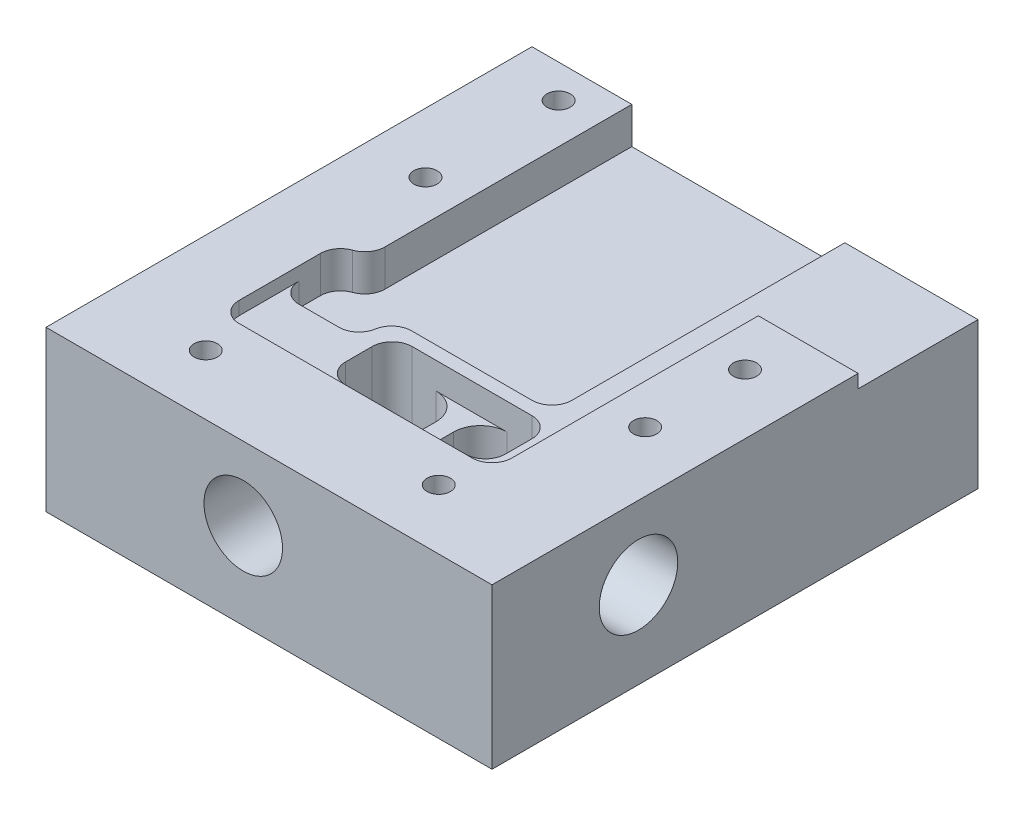
SolidWorks part; units mm, degrees
ref_plane "Front" through (0, 0, 0) normal (0, 0, 1) x (1, 0, 0)
ref_plane "Top" through (0, 0, 0) normal (0, 1, 0) x (1, 0, 0)
ref_plane "Right" through (0, 0, 0) normal (1, 0, 0) x (0, 0, -1)
sketch "Sketch1" plane through (0, 0, 0) normal (0, 1, 0) x (1, 0, 0)
  line L1 (0, 0) -> (67, 0)
  line L2 (0, 0) -> (0, 73)
  line L3 (0, 73) -> (67, 73)
  line L4 (67, 0) -> (67, 73)
  dimension "D1" = 73
  dimension "D2" = 67
extrude "Boss-Extrude1" add sketch "Sketch1" along normal blind 15
sketch "Sketch5" plane through (0, 15, 0) normal (0, 1, 0) x (1, 0, 0)
  line L0 (18.5, 15) -> (11, 15)
  line L1 (32, 15) -> (52, 15)
  line L2 (47, 73) -> (47, 29)
  line L3 (47, 73) -> (52, 73)
  line L4 (52, 15) -> (52, 73)
  line L5 (47, 29) -> (23, 29)
  line L7 (0, 0) -> (67, 0) construction
  line L8 (11, 24) -> (14.7889, 24)
  line L9 (67, 0) -> (67, 73) construction
  line L10 (11, 15) -> (11, 24)
  line L11 (18.5, 15) -> (32, 15)
  line L12 (23, 29) -> (23, 27)
  line L13 (20, 24) -> (14.7889, 24)
  arc A0 (23, 27) -> (20, 24) centre (20, 27) cw
  point P17 (17.932, 24.0268)
  point P19 (18.3944, 28)
  dimension "D6" = 14
  dimension "D5" = 3
  dimension "D1" = 5
  dimension "D2" = 58
  dimension "D3" = 15
  dimension "D4" = 15
  dimension "D7" = 41
  dimension "D8" = 9
  dimension "D10" = 24
extrude "Boss-Extrude2" add sketch "Sketch5" along normal blind 3.5
sketch "Sketch6" plane through (0, 18.5, 0) normal (0, 1, 0) x (1, 0, 0)
  line L1 (25, 27) -> (49, 27)
  line L2 (25, 27) -> (25, 17)
  line L3 (25, 17) -> (49, 17)
  line L4 (49, 27) -> (49, 17)
  line L6 (47, 29) -> (23, 29) construction
  line L8 (11, 15) -> (52, 15) construction
  line L13 (52, 15) -> (52, 73) construction
  dimension "D1" = 2
  dimension "D2" = 2
  dimension "D3" = 24
  dimension "D4" = 3
extrude "Cut-Extrude2" cut sketch "Sketch6" against normal blind 16
sketch "Sketch8" plane through (0, 0, -17) normal (0, 0, -1) x (-1, 0, 0)
  line L4 (-49, 2.5) -> (-25, 2.5)
  line L5 (-25, 18.5) -> (-49, 18.5)
  line L6 (-49, 18.5) -> (-49, 2.5)
  line L7 (-49, 2.5) -> (-25, 2.5)
  line L8 (-25, 2.5) -> (-25, 18.5)
  line L9 (-25, 18.5) -> (-49, 18.5)
  line L10 (-49, 18.5) -> (-49, 2.5) construction
  line L12 (-25, 2.5) -> (-25, 18.5) construction
  circle A0 centre (-42, 6.1554) radius 4
  dimension "D1" = 8
  dimension "D4" = 7
extrude "Cut-Extrude4" [suppressed] cut sketch "Sketch8" against normal through all contours A0
sketch "Sketch9" plane through (49, 0, 0) normal (-1, 0, 0) x (0, 0, 1)
  line L4 (-17, 18.5) -> (-27, 18.5)
  line L5 (-27, 18.5) -> (-27, 2.5)
  line L6 (-27, 2.5) -> (-17, 2.5)
  line L7 (-17, 2.5) -> (-17, 18.5)
  line L8 (-17, 18.5) -> (-27, 18.5)
  line L9 (-27, 18.5) -> (-27, 2.5) construction
  line L10 (-27, 2.5) -> (-17, 2.5)
  line L11 (-17, 2.5) -> (-17, 18.5) construction
  circle A0 centre (-22, 5.8531) radius 4
  dimension "D2" = 8
  dimension "D3" = 5
extrude "Cut-Extrude5" [suppressed] cut sketch "Sketch9" against normal through all contours A0
sketch "Sketch11" plane through (0, 0, 0) normal (0, -1, 0) x (1, 0, 0)
  line L1 (0, 0) -> (67, 0)
  line L2 (0, 0) -> (0, -73)
  line L3 (0, -73) -> (67, -73)
  line L4 (67, 0) -> (67, -73)
extrude "Boss-Extrude4" add sketch "Sketch11" along normal blind 3.5
sketch "Sketch12" plane through (0, 15, 0) normal (0, 1, 0) x (1, 0, 0)
  line L0 (18.4556, 68) -> (48.6562, 68) construction
  line L1 (18.4556, 68) -> (18.4556, 18.1652) construction
  line L2 (67, 73) -> (52, 73) construction
  line L3 (67, 0) -> (67, 73) construction
  circle A0 centre (18.4556, 68) radius 1.025
  circle A2 centre (48.6562, 68) radius 1.025
  circle A4 centre (36.6635, 53.2215) radius 1.38 construction
  circle A6 centre (18.4556, 18.1652) radius 1.025
  dimension "D1" = 2.05
  dimension "D2" = 30.2006
  dimension "D3" = 49.8348
  dimension "D4" = 5
  dimension "D5" = 18.3438
sketch "Sketch13" plane through (0, 15, 0) normal (0, 1, 0) x (1, 0, 0)
  line L1 (52, 15) -> (67, 15)
  line L2 (52, 15) -> (52, 55)
  line L3 (52, 55) -> (67, 55)
  line L4 (67, 15) -> (67, 55)
  line L5 (11, 15) -> (52, 15) construction
  line L7 (67, 0) -> (67, 73) construction
  dimension "D1" = 15
  dimension "D2" = 40
extrude "Boss-Extrude6" add sketch "Sketch13" along normal blind 5.5
sketch "Sketch16" [suppressed] plane through (0, 0, 0) normal (0, 0, 1) x (1, 0, 0)
  circle A0 centre (57, 6.1554) radius 5.9
  circle A1 centre (57, 6.1554) radius 4 construction
  circle A2 centre (57, 6.1554) radius 4 construction
  dimension "D1" = 11.8
extrude "Cut-Extrude8" [suppressed] cut sketch "Sketch16" against normal blind 10
sketch "Sketch17" [suppressed] plane through (67, 0, 0) normal (1, 0, 0) x (0, 0, -1)
  circle A0 centre (65, 5.8531) radius 4 construction
  circle A1 centre (65, 5.8531) radius 4 construction
  circle A2 centre (65, 5.8531) radius 5.9
  dimension "D1" = 11.8
extrude "Cut-Extrude9" [suppressed] cut sketch "Sketch17" against normal blind 10
sketch "Sketch14" plane through (0, 20.5, 0) normal (0, 1, 0) x (1, 0, 0)
  line L0 (67, 15) -> (67, 55) construction
  line L1 (67, 55) -> (52, 55) construction
  circle A0 centre (58, 47) radius 1.75
  circle A1 centre (58, 32) radius 1.75
  dimension "D1" = 3.5
  dimension "D2" = 15
  dimension "D3" = 9
  dimension "D4" = 8
extrude "Cut-Extrude7" cut sketch "Sketch14" against normal blind 10
sketch "Sketch18" plane through (0, 15, 0) normal (0, 1, 0) x (1, 0, 0)
  line L0 (15, 33.2378) -> (15, 73)
  line L1 (67, 15) -> (15, 15)
  line L2 (67, 15) -> (67, 0)
  line L3 (67, 0) -> (0, 0)
  line L4 (0, 15) -> (0, 0)
  line L5 (67, 73) -> (52, 73) construction
  line L6 (15, 73) -> (0, 73)
  line L7 (0, 73) -> (0, 15)
  line L8 (52, 15) -> (52, 55) construction
  line L9 (15, 33.2378) -> (14, 33.2378)
  line L10 (11, 30.2378) -> (11, 17.9921)
  line L12 (13.7825, 15) -> (15, 15)
  arc A0 (14, 33.2378) -> (11, 30.2378) centre (14, 30.2378) ccw
  arc A1 (11, 17.9921) -> (13.7825, 15) centre (14, 17.9921) ccw
  dimension "D2" = 3
  dimension "D1" = 37
  dimension "D3" = 4
extrude "Boss-Extrude7" add sketch "Sketch18" along normal up to surface (5.5 mm away) up to face at (58, 20.5, -30.25)
sketch "Sketch19" plane through (0, 20.5, 0) normal (0, 1, 0) x (1, 0, 0)
  line L0 (9, 68) -> (9, 48) construction
  line L1 (67, 0) -> (0, 0) construction
  line L3 (15, 73) -> (15, 33.2378) construction
  line L4 (52, 15) -> (13.7825, 15) construction
  line L5 (15, 9) -> (50, 9) construction
  line L6 (0, 0) -> (0, 73) construction
  circle A0 centre (9, 48) radius 1.75
  circle A1 centre (9, 68) radius 1.75
  circle A2 centre (15, 9) radius 1.75
  circle A3 centre (50, 9) radius 1.75
  dimension "D1" = 3.5
  dimension "D2" = 3.5
  dimension "D6" = 3.5
  dimension "D7" = 3.5
  dimension "D3" = 20
  dimension "D5" = 6
  dimension "D8" = 35
  dimension "D10" = 15
  dimension "D9" = 9
  dimension "D4" = 33
fillet "Fillet5" radius 3 1 edges at (52, 19.5, -15)
sketch "Sketch20" plane through (0, 15, 0) normal (0, 1, 0) x (1, 0, 0)
  line L4 (52, 55) -> (67, 55)
  line L5 (52, 55) -> (67, 55)
  line L6 (67, 73) -> (52, 73)
  line L7 (67, 55) -> (67, 73)
  line L8 (67, 55) -> (67, 73)
  line L9 (52, 73) -> (52, 55)
  line L10 (67, 73) -> (52, 73)
  line L11 (52, 73) -> (52, 55)
  dimension "D1" = 0
extrude "Boss-Extrude8" add sketch "Sketch20" along normal up to surface (3.5 mm away) up to face at (37, 18.5, -22)
fillet "Fillet10" radius 3 1 edges at (47, 16.75, -29)
fillet "Fillet11" radius 3 2 edges at (23, 16.75, -29) (11, 16.75, -24)
fillet "Fillet12" radius 3 1 edges at (15, 17.75, -33.2378)
fillet "Fillet13" radius 3 4 edges at (25, 10.5, -27) (25, 10.5, -17) (49, 10.5, -27) (49, 10.5, -17)
sketch "Sketch21" plane through (0, 2.5, 0) normal (0, 1, 0) x (1, 0, 0)
  line L0 (46, 27) -> (28, 27) construction
  line L1 (35.5807, 27) -> (38.2299, 27)
  line L2 (35.5807, 27) -> (35.5807, 17)
  line L3 (35.5807, 17) -> (38.2299, 17)
  line L4 (38.2299, 27) -> (38.2299, 17)
  line L5 (28, 17) -> (46, 17) construction
extrude "Boss-Extrude9" add sketch "Sketch21" along normal blind 12
fillet "Fillet15" radius 4 4 edges at (35.5807, 8.5, -27) (38.2299, 8.5, -27) (38.2299, 8.5, -17) (35.5807, 8.5, -17)
extrude "Cut-Extrude11" cut sketch "Sketch19" against normal blind 10
sketch "Sketch23" plane through (49, 0, 0) normal (-1, 0, 0) x (0, 0, 1)
  line L0 (-20, 2.5) -> (-24, 2.5) construction
  line L1 (-22, 18.5) -> (-22, 2.5) construction
  line L2 (-20, 18.5) -> (-24, 18.5) construction
  circle A0 centre (-22, 9.5) radius 4
  point P4 (-22, 2.5)
  dimension "D1" = 8
  dimension "D2" = 7
extrude "Cut-Extrude12" cut sketch "Sketch23" against normal through all and the other way blind 2
sketch "Sketch24" plane through (67, 0, 0) normal (1, 0, 0) x (0, 0, -1)
  circle A0 centre (22, 9.5) radius 5.9
  dimension "D1" = 11.8
extrude "Cut-Extrude13" cut sketch "Sketch24" against normal blind 10
sketch "Sketch25" plane through (0, 0, -17) normal (0, 0, -1) x (-1, 0, 0)
  line L0 (-28, 2.5) -> (-31.5807, 2.5) construction
  circle A0 centre (-29.6283, 9.5) radius 4
  dimension "D1" = 8
  dimension "D2" = 7
extrude "Cut-Extrude14" cut sketch "Sketch25" against normal through all and the other way blind 2
sketch "Sketch26" plane through (0, 0, 0) normal (0, 0, 1) x (1, 0, 0)
  circle A0 centre (29.6283, 9.5) radius 5.9
  dimension "D1" = 11.8
extrude "Cut-Extrude15" cut sketch "Sketch26" against normal blind 10
ref_plane "Plane1" through (52, 18.5, -55) normal (0, -1, 0) x (-1, 0, 0)
equation "\"d_racor\"= 11.8"
equation "\"h_alphasense\"= 5"
equation "\"h_chamber\"= 13"
equation "\"d_alphasense\"= 32.4mm"
equation "\"d_chamber\"= 19"
equation "\"h_base\"= 25 - \"h_chamber\" - \"h_alphasense\"-1"
equation "\"length_thread\"=10"
equation "\"D2@Sketch9\"=\"d_pipe\""
equation "\"D1@Sketch8\"=\"d_pipe\""
equation "\"length_racor\"= 10"
equation "\"d_pipe\"=8"
equation "\"D1@Sketch12\"= \"d_thread_sck_tap\""
equation "\"D1@Sketch16\"=\"d_racor\""
equation "\"D1@Cut-Extrude8\"=\"length_racor\""
equation "\"D1@Sketch17\"=\"d_racor\""
equation "\"D1@Cut-Extrude9\"=\"length_racor\""
equation "\"clip_thread_hole\"= 4"
equation "\"clip_thread_tap_drill\"= 3.5"
equation "\"D1@Sketch14\"=\"clip_thread_tap_drill\""
equation "\"D1@Cut-Extrude7\"=\"length_thread\""
equation "\"d_thread_sck_hole\"= 2.5"
equation "\"d_thread_sck_tap\"= 2.05"
equation "\"D1@Sketch19\"=\"clip_thread_tap_drill\""
equation "\"D2@Sketch19\"=\"clip_thread_tap_drill\""
equation "\"D6@Sketch19\"=\"clip_thread_tap_drill\""
equation "\"D7@Sketch19\"=\"clip_thread_tap_drill\""
equation "\"D1@Cut-Extrude11\"=\"length_thread\""
equation "\"D1@Sketch23\"=\"d_pipe\""
equation "\"D1@Sketch24\"=\"d_racor\""
equation "\"D1@Sketch25\"=\"d_pipe\""
equation "\"D1@Cut-Extrude15\"=\"length_racor\""
equation "\"D1@Cut-Extrude13\"=\"length_racor\""
